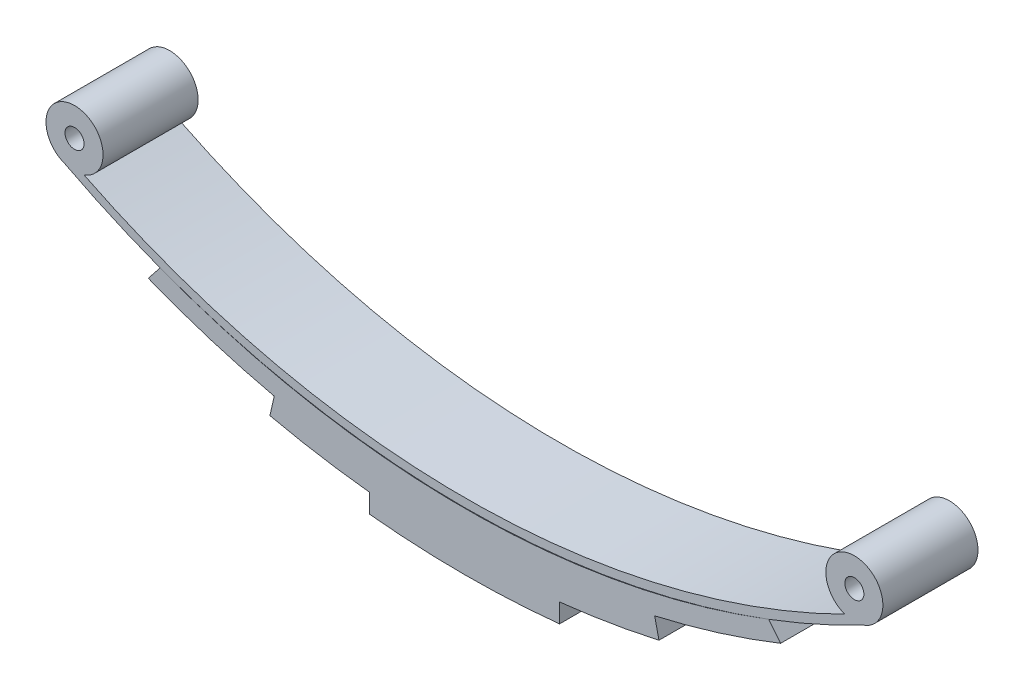
SolidWorks part; units mm, degrees
ref_plane "Front Plane" through (0, 0, 0) normal (0, 0, 1) x (1, 0, 0)
ref_plane "Top Plane" through (0, 0, 0) normal (0, 1, 0) x (1, 0, 0)
ref_plane "Right Plane" through (0, 0, 0) normal (1, 0, 0) x (0, 0, -1)
sketch "Sketch1" plane through (0, 0, 0) normal (0, 0, 1) x (1, 0, 0)
  line L0 (0, 91.307) -> (0, -34.5864) construction
  line L1 (-93.9047, 0) -> (97.6861, 0) construction
  arc A0 (-40, 0) -> (40, 0) centre (0, 80.6226) ccw
  arc A1 (-42, 0) -> (42, 0) centre (0, 80.6226) ccw
  arc A2 (-42, 0) -> (-40, 0) centre (-41, 2.8284) cw
  arc A3 (40, 0) -> (42, 0) centre (41, 2.8284) cw
  circle A4 centre (-41, 2.8284) radius 1
  circle A5 centre (41, 2.8284) radius 1
  dimension "D1" = 90
  dimension "D3" = 3
  dimension "D4" = 3
  dimension "D5" = 2
  dimension "D6" = 2
  dimension "D2" = 42
extrude "Boss-Extrude1" add sketch "Sketch1" along normal blind 10
sketch "Sketch2" plane through (0, 0, 0) normal (0, 0, 1) x (1, 0, 0)
  line L0 (0, 30.1447) -> (0, -39.3254) construction
  line L1 (-33.2459, -6.0301) -> (-32, -4.4656)
  line L2 (32, -4.4656) -> (33.2459, -6.0301)
  arc A1 (-42, 0) -> (42, 0) centre (0, 80.6226) ccw construction
  arc A4 (-32, -4.4656) -> (32, -4.4656) centre (0, 79.6534) ccw
  arc A5 (-33.2459, -6.0301) -> (33.2459, -6.0301) centre (0, 77.6043) ccw
  dimension "D5" = 90
  dimension "D6" = 90
  dimension "D1" = 32
  dimension "D2" = 32
  dimension "D3" = 2
  dimension "D4" = 2
extrude "Boss-Extrude3" add sketch "Sketch2" along normal blind 10 separate body
sketch "Sketch3" plane through (0, 0, 0) normal (0, 0, 1) x (1, 0, 0)
  line L2 (-20, -10.1454) -> (-20.4558, -12.1454)
  line L3 (20, -10.1454) -> (20.4558, -12.1454)
  arc A0 (-20, -10.1454) -> (20, -10.1454) centre (0, 77.6043) ccw
  arc A1 (-33.2459, -6.0301) -> (33.2459, -6.0301) centre (0, 77.6043) ccw construction
  arc A3 (-20.4558, -12.1454) -> (20.4558, -12.1454) centre (0, 78.577) ccw
  dimension "D3" = 93
  dimension "D4" = 2
  dimension "D1" = 20
  dimension "D2" = 20
  dimension "D5" = 2
extrude "Boss-Extrude5" add sketch "Sketch3" along normal blind 10
sketch "Sketch4" plane through (0, 0, 0) normal (0, 0, 1) x (1, 0, 0)
  line L2 (-10, -13.8838) -> (-10, -15.8838)
  line L3 (10, -13.8838) -> (10, -15.8838)
  arc A0 (-10, -13.8838) -> (10, -13.8838) centre (0, 78.577) ccw
  arc A1 (-20.4558, -12.1454) -> (20.4558, -12.1454) centre (0, 78.577) ccw construction
  arc A3 (-10, -15.8838) -> (10, -15.8838) centre (0, 81.6047) ccw
  dimension "D3" = 2
  dimension "D5" = 98
  dimension "D1" = 10
  dimension "D2" = 10
  dimension "D4" = 2
extrude "Boss-Extrude12" add sketch "Sketch4" along normal through all
